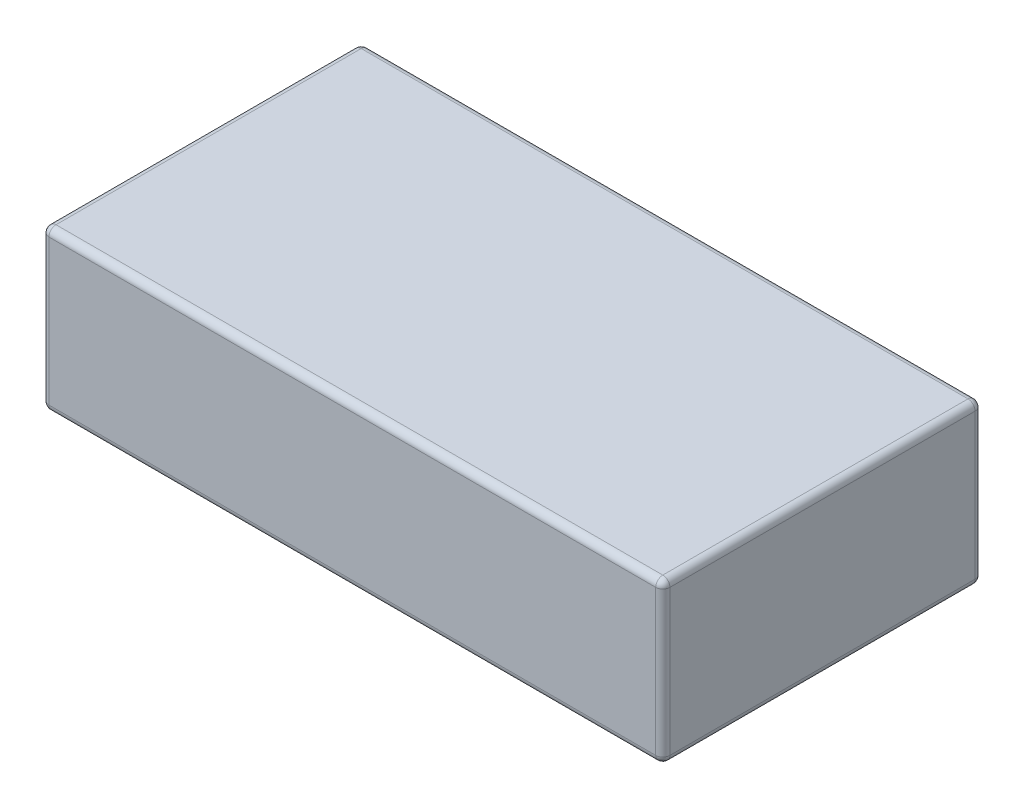
SolidWorks part; units mm, degrees
material "1060 Alloy"
ref_plane "Front Plane" through (0, 0, 0) normal (0, 0, 1) x (1, 0, 0)
ref_plane "Top Plane" through (0, 0, 0) normal (0, 1, 0) x (1, 0, 0)
ref_plane "Right Plane" through (0, 0, 0) normal (1, 0, 0) x (0, 0, -1)
sketch "Sketch1" plane through (0, 0, 0) normal (0, 0, 1) x (1, 0, 0)
  line L1 (-87.5, 22.5) -> (87.5, 22.5)
  line L2 (-87.5, 22.5) -> (-87.5, -22.5)
  line L3 (-87.5, -22.5) -> (87.5, -22.5)
  line L4 (87.5, 22.5) -> (87.5, -22.5)
  line L5 (-87.5, 22.5) -> (87.5, -22.5) construction
  line L6 (-87.5, -22.5) -> (87.5, 22.5) construction
  point P0 (0, 0)
  dimension "D1" = 175
  dimension "D2" = 45
extrude "Boss-Extrude1" add sketch "Sketch1" along normal blind 90
fillet "Fillet1" radius 2 12 edges at (0, -22.5, 90) (0, -22.5, 0) (-87.5, 0, 90) (-87.5, -22.5, 45) (-87.5, 0, 0) (0, 22.5, 90) (-87.5, 22.5, 45) (0, 22.5, 0) (87.5, -22.5, 45) (87.5, 0, 90) (87.5, 22.5, 45) (87.5, 0, 0)
